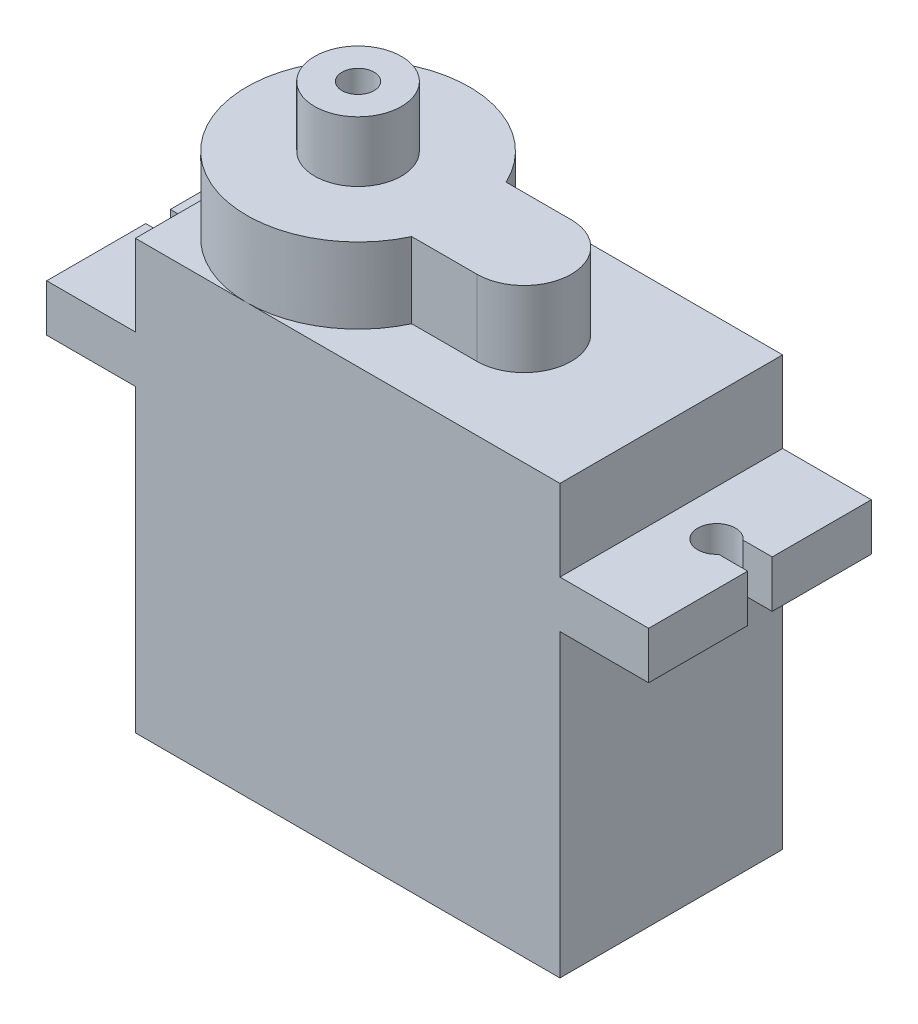
SolidWorks part; units mm, degrees
ref_plane "Front Plane" through (0, 0, 0) normal (0, 0, 1) x (1, 0, 0)
ref_plane "Top Plane" through (0, 0, 0) normal (0, 1, 0) x (1, 0, 0)
ref_plane "Right Plane" through (0, 0, 0) normal (1, 0, 0) x (0, 0, -1)
sketch "Sketch2" plane through (0, 0, 0) normal (0, 0, 1) x (1, 0, 0)
  line L1 (11.25, -11.35) -> (-11.25, -11.35)
  line L2 (11.25, -11.35) -> (11.25, 11.35)
  line L3 (11.25, 11.35) -> (-11.25, 11.35)
  line L4 (-11.25, -11.35) -> (-11.25, 11.35)
  line L5 (11.25, -11.35) -> (-11.25, 11.35) construction
  line L6 (11.25, 11.35) -> (-11.25, -11.35) construction
  point P0 (0, 0)
  dimension "D1" = 22.7
  dimension "D2" = 22.5
extrude "Boss-Extrude1" add sketch "Sketch2" along normal mid plane 11.8
ref_plane "Plane1" through (0, 4.55, 0) normal (0, -1, 0) x (-1, 0, 0)
sketch "Sketch3" plane through (0, 4.55, 0) normal (0, -1, 0) x (-1, 0, 0)
  line L0 (14.4099, 0.65) -> (15.95, 0.65)
  line L1 (-11.25, -5.9) -> (-15.95, -5.9)
  line L2 (-11.25, -5.9) -> (-11.25, 5.9)
  line L3 (-11.25, 5.9) -> (-15.95, 5.9)
  line L4 (-15.95, -5.9) -> (-15.95, -0.65)
  line L5 (11.25, -5.9) -> (15.95, -5.9)
  line L6 (11.25, -5.9) -> (11.25, 5.9)
  line L7 (11.25, 5.9) -> (15.95, 5.9)
  line L8 (15.95, -5.9) -> (15.95, -0.65)
  line L9 (15.95, 0) -> (-15.95, 0) construction
  line L10 (15.95, -0.65) -> (14.4099, -0.65)
  line L11 (15.95, 0.65) -> (15.95, 5.9)
  line L15 (-15.95, -0.65) -> (-14.4099, -0.65)
  line L16 (-14.4099, 0.65) -> (-15.95, 0.65)
  line L17 (-15.95, 0.65) -> (-15.95, 5.9)
  arc A0 (14.4099, 0.65) -> (14.4099, -0.65) centre (13.65, 0) ccw
  arc A1 (-14.4099, 0.65) -> (-14.4099, -0.65) centre (-13.65, 0) cw
  dimension "D3" = 2
  dimension "D1" = 4.7
  dimension "D2" = 4.7
  dimension "D5" = 0.65
  dimension "D6" = 1.3
extrude "Boss-Extrude2" add sketch "Sketch3" against normal blind 2.5
sketch "Sketch4" plane through (0, 11.35, 0) normal (0, 1, 0) x (1, 0, 0)
  line L0 (-11.25, 5.9) -> (-11.25, -5.9) construction
  line L1 (-5.35, 0) -> (3.45, 0) construction
  line L2 (3.45, 2.5) -> (-0.0058, 2.5)
  line L3 (3.45, -2.5) -> (-0.0058, -2.5)
  arc A0 (-0.0058, 2.5) -> (-0.0058, -2.5) centre (-5.35, 0) ccw
  arc A1 (3.45, -2.5) -> (3.45, 2.5) centre (3.45, 0) ccw
  dimension "D1" = 11.8
  dimension "D3" = 5
  dimension "D2" = 8.8
extrude "Boss-Extrude3" add sketch "Sketch4" along normal blind 4
sketch "Sketch5" plane through (0, 15.35, 0) normal (0, 1, 0) x (1, 0, 0)
  circle A0 centre (-5.35, 0) radius 0.85
  circle A1 centre (-5.35, 0) radius 2.3
  dimension "D1" = 1.7
  dimension "D2" = 4.6
extrude "Boss-Extrude4" add sketch "Sketch5" along normal blind 3.2
